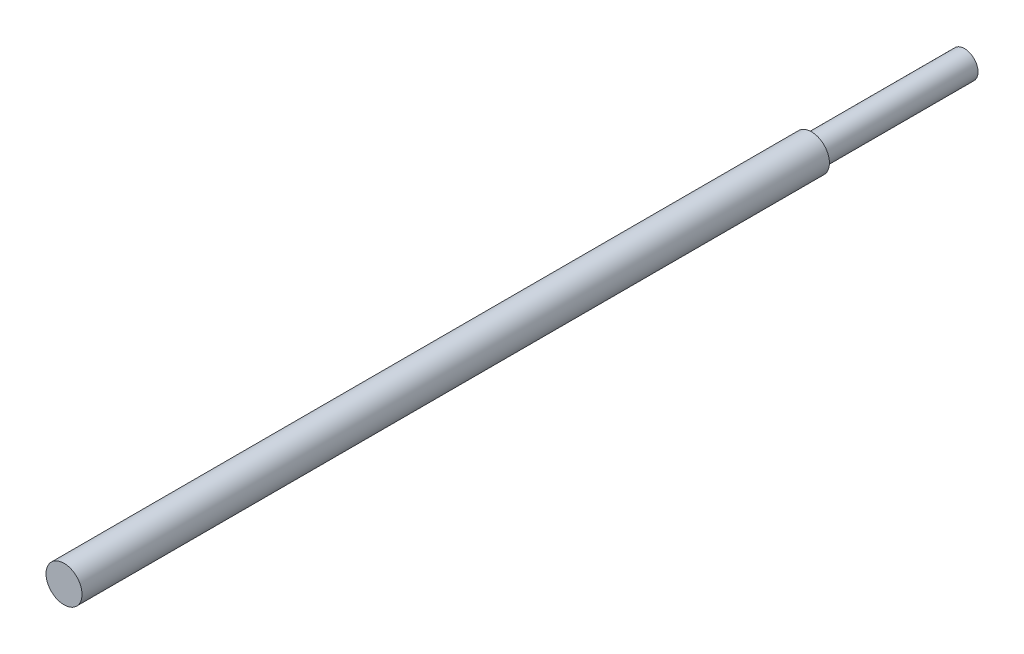
SolidWorks part; units mm, degrees
ref_plane "Front Plane" through (0, 0, 0) normal (0, 0, 1) x (1, 0, 0)
ref_plane "Top Plane" through (0, 0, 0) normal (0, 1, 0) x (1, 0, 0)
ref_plane "Right Plane" through (0, 0, 0) normal (1, 0, 0) x (0, 0, -1)
sketch "Sketch1" plane through (0, 0, 0) normal (0, 0, 1) x (1, 0, 0)
  circle A0 centre (0, 0) radius 8
  dimension "D1" = 16
extrude "Boss-Extrude1" add sketch "Sketch1" along normal blind 400
sketch "Sketch2" plane through (0, 0, 0) normal (0, 0, -1) x (-1, 0, 0)
  circle A0 centre (0, 0) radius 6
  circle A1 centre (0, 0) radius 10.6662
  dimension "D1" = 12
extrude "Cut-Extrude1" cut sketch "Sketch2" against normal blind 68
